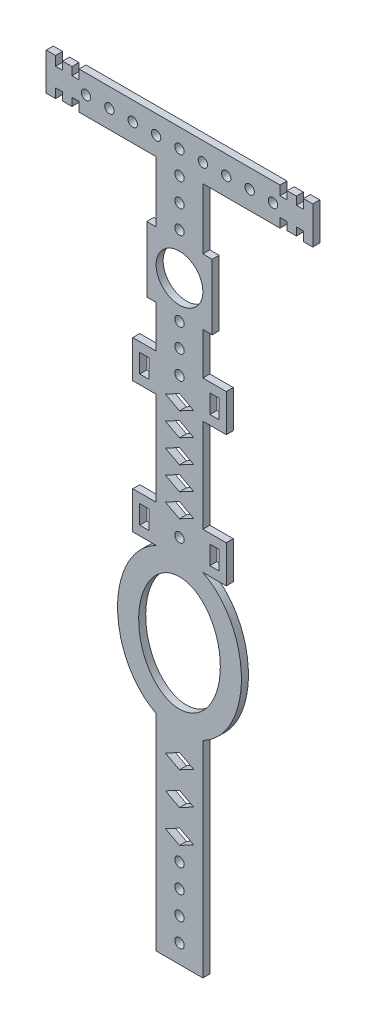
SolidWorks part; units mm, degrees
ref_plane "前视基准面" through (0, 0, 0) normal (0, 0, 1) x (1, 0, 0)
ref_plane "上视基准面" through (0, 0, 0) normal (0, 1, 0) x (1, 0, 0)
ref_plane "右视基准面" through (0, 0, 0) normal (1, 0, 0) x (0, 0, -1)
other "Configuration Table"
sketch "草图1" plane through (0, 0, 0) normal (0, 0, 1) x (1, 0, 0)
  line L0 (-21.4993, 30) -> (-21.4993, 28)
  line L1 (-21.4993, 28) -> (-22.9993, 28)
  line L2 (-22.9993, 29.7) -> (-24.9993, 29.7)
  line L3 (-7, 9) -> (-5, 9)
  line L4 (-7, 9) -> (-7, -5)
  line L5 (-7, -5) -> (-5, -5)
  line L6 (7, 9) -> (7, -5)
  line L7 (-7, 9) -> (7, -5) construction
  line L8 (-7, -5) -> (7, 9) construction
  line L9 (-24.9993, 29.7) -> (-24.9993, 28)
  line L10 (-26.4993, 28) -> (-26.4993, 30.4519)
  line L11 (2.9879, -40.9786) -> (-0.0121, -42.582)
  line L12 (-26.4993, 30) -> (-28.4993, 30)
  line L13 (-28.4993, 30) -> (-28.4993, 22)
  line L18 (-22.9993, 24) -> (-22.9993, 22.3)
  line L19 (-26.4993, 24) -> (-24.9993, 24)
  line L20 (0, -0.8258) -> (0, -11.7354) construction
  line L21 (-5, 9) -> (-5, 22)
  line L22 (-5, 22) -> (-21.4993, 22)
  line L23 (-26.4993, 22) -> (-28.4993, 22)
  line L24 (-26.4993, 24) -> (-26.4993, 22)
  line L25 (-0.0121, -42.582) -> (-3.0121, -40.9786)
  line L26 (-24.9993, 22.3) -> (-24.9993, 24)
  line L27 (-22.9993, 22.3) -> (-24.9993, 22.3)
  line L29 (-21.4993, 24) -> (-22.9993, 24)
  line L30 (-21.4993, 22) -> (-21.4993, 24)
  line L35 (22.9993, 28) -> (22.9993, 29.7)
  line L36 (26.4993, 28) -> (24.9993, 28)
  line L42 (-26.4993, 28) -> (-24.9993, 28)
  line L43 (-22.9993, 28) -> (-22.9993, 29.7)
  line L46 (21.4993, 22) -> (21.4993, 24)
  line L47 (21.4993, 24) -> (22.9993, 24)
  line L48 (-21.4993, 30) -> (21.4993, 30)
  line L49 (-5, -5) -> (-5, -14)
  line L50 (-5, -14) -> (-10, -14)
  line L51 (-10, -14) -> (-10, -22)
  line L52 (-10, -22) -> (-5, -22)
  line L53 (-5, -22) -> (-5, -42)
  line L54 (-5, -42) -> (-10, -42)
  line L55 (-10, -42) -> (-10, -50)
  line L56 (-10, -50) -> (-5, -50)
  line L57 (-8.5, -16) -> (-6.5, -16)
  line L58 (-8.5, -16) -> (-8.5, -20)
  line L59 (-8.5, -20) -> (-6.5, -20)
  line L60 (-6.5, -16) -> (-6.5, -20)
  line L61 (-8.5, -16) -> (-6.5, -20) construction
  line L62 (-8.5, -20) -> (-6.5, -16) construction
  line L63 (-8.5, -44) -> (-6.5, -44)
  line L64 (-8.5, -44) -> (-8.5, -48)
  line L65 (-8.5, -48) -> (-6.5, -48)
  line L66 (-6.5, -44) -> (-6.5, -48)
  line L67 (-8.5, -44) -> (-6.5, -48) construction
  line L68 (-8.5, -48) -> (-6.5, -44) construction
  line L69 (5, 9) -> (5, 22)
  line L70 (22.9993, 22.3) -> (24.9993, 22.3)
  line L71 (24.9993, 22.3) -> (24.9993, 24)
  line L72 (26.4993, 24) -> (26.4993, 22)
  line L73 (-3.0121, -40.9786) -> (-0.0121, -39.3752)
  line L74 (26.4993, 22) -> (28.4993, 22)
  line L75 (26.4993, 24) -> (24.9993, 24)
  line L76 (22.9993, 24) -> (22.9993, 22.3)
  line L77 (28.4993, 30) -> (28.4993, 22)
  line L78 (26.4993, 30) -> (28.4993, 30)
  line L79 (5, 22) -> (21.4993, 22)
  line L80 (5, -5) -> (5, -14)
  line L81 (8.5, -48) -> (6.5, -44) construction
  line L82 (8.5, -44) -> (6.5, -48) construction
  line L83 (8.5, -20) -> (6.5, -16) construction
  line L84 (8.5, -16) -> (6.5, -20) construction
  line L85 (6.5, -44) -> (6.5, -48)
  line L86 (8.5, -48) -> (6.5, -48)
  line L87 (8.5, -44) -> (8.5, -48)
  line L88 (8.5, -44) -> (6.5, -44)
  line L89 (6.5, -16) -> (6.5, -20)
  line L90 (8.5, -20) -> (6.5, -20)
  line L91 (8.5, -16) -> (8.5, -20)
  line L92 (8.5, -16) -> (6.5, -16)
  line L93 (10, -50) -> (5, -50)
  line L94 (10, -42) -> (10, -50)
  line L95 (5, -42) -> (10, -42)
  line L96 (5, -22) -> (5, -42)
  line L97 (10, -22) -> (5, -22)
  line L98 (10, -14) -> (10, -22)
  line L99 (5, -14) -> (10, -14)
  line L100 (-5, -81.1196) -> (-5, -125.1196)
  line L101 (-0.0121, -39.3752) -> (2.9879, -40.9786)
  line L102 (5, -125.1196) -> (5, -81.1196)
  line L107 (3, -101.4579) -> (0, -103.0613)
  line L108 (0, -103.0613) -> (-3, -101.4579)
  line L109 (-3, -101.4579) -> (0, -99.8545)
  line L110 (0, -99.8545) -> (3, -101.4579)
  line L111 (3, -94.4579) -> (0, -96.0613)
  line L112 (0, -96.0613) -> (-3, -94.4579)
  line L113 (-3, -94.4579) -> (0, -92.8545)
  line L114 (0, -92.8545) -> (3, -94.4579)
  line L115 (3, -87.4579) -> (0, -89.0613)
  line L116 (0, -89.0613) -> (-3, -87.4579)
  line L117 (-3, -87.4579) -> (0, -85.8545)
  line L118 (0, -85.8545) -> (3, -87.4579)
  line L119 (-5, -125.1196) -> (5, -125.1196)
  line L120 (-27.5, 26) -> (-15.7949, 26) construction
  line L121 (26.4993, 28) -> (26.4993, 30)
  line L122 (2.9879, -35.9786) -> (-0.0121, -37.582)
  line L123 (24.9993, 29.7) -> (24.9993, 28)
  line L124 (22.9993, 29.7) -> (24.9993, 29.7)
  line L125 (21.4993, 28) -> (22.9993, 28)
  line L126 (21.4993, 30) -> (21.4993, 28)
  line L127 (5, -5) -> (7, -5)
  line L128 (5, 9) -> (7, 9)
  line L129 (-0.0121, -37.582) -> (-3.0121, -35.9786)
  line L130 (-3.0121, -35.9786) -> (-0.0121, -34.3752)
  line L131 (-0.0121, -34.3752) -> (2.9879, -35.9786)
  line L132 (2.9879, -30.9786) -> (-0.0121, -32.582)
  line L133 (-0.0121, -32.582) -> (-3.0121, -30.9786)
  line L134 (-3.0121, -30.9786) -> (-0.0121, -29.3752)
  line L135 (-0.0121, -29.3752) -> (2.9879, -30.9786)
  line L136 (2.9879, -25.9786) -> (-0.0121, -27.582)
  line L137 (-0.0121, -27.582) -> (-3.0121, -25.9786)
  line L138 (-3.0121, -25.9786) -> (-0.0121, -24.3752)
  line L139 (-0.0121, -24.3752) -> (2.9879, -25.9786)
  line L140 (2.9879, -20.9786) -> (-0.0121, -22.582)
  line L141 (-0.0121, -22.582) -> (-3.0121, -20.9786)
  line L142 (-3.0121, -20.9786) -> (-0.0121, -19.3752)
  line L143 (-0.0121, -19.3752) -> (2.9879, -20.9786)
  circle A0 centre (0, 2) radius 5
  circle A2 centre (0, -121.1196) radius 1
  circle A3 centre (0, -116.1196) radius 1
  circle A4 centre (0, -46) radius 1
  circle A10 centre (0, -16) radius 1
  circle A11 centre (0, -11) radius 1
  circle A12 centre (0, -6) radius 1
  circle A13 centre (0, 25.9514) radius 1
  circle A14 centre (5, 25.9514) radius 1
  circle A15 centre (10, 25.9514) radius 1
  circle A16 centre (15, 25.9514) radius 1
  circle A17 centre (20, 25.9514) radius 1
  circle A18 centre (-5, 25.9514) radius 1
  circle A19 centre (-10, 25.9514) radius 1
  circle A20 centre (-15, 25.9514) radius 1
  circle A21 centre (-20, 25.9514) radius 1
  circle A22 centre (0, 20.9514) radius 1
  circle A23 centre (0, 15.9514) radius 1
  circle A24 centre (0, 10.9514) radius 1
  circle A25 centre (0, -111.1196) radius 1
  circle A26 centre (0, -106.1196) radius 1
  circle A27 centre (0, -41) radius 1 [skipped]
  circle A28 centre (0, -36) radius 1 [skipped]
  circle A29 centre (0, -31) radius 1 [skipped]
  circle A30 centre (0, -26) radius 1 [skipped]
  circle A31 centre (0, -21) radius 1 [skipped]
  ellipse E0 centre (0, -65.5598) end of major axis (0, -77.8215) minor radius 8.7277
  spline S1 degree 3 poles (-2.9572, -82.0581) (0, -82.472) (2.9572, -82.0581) (6.5802, -80.4965) (10.1362, -77.0656) (12.461, -72.0885) (13.2579, -67.5921) (13.2579, -63.5275) (12.461, -59.0311) (10.1362, -54.0539) (6.5802, -50.6231) (2.9572, -49.0614) (0, -48.6476) (-2.9572, -49.0614) (-6.5802, -50.6231) (-10.1362, -54.0539) (-12.461, -59.0311) (-13.2579, -63.5275) (-13.2579, -67.5921) (-12.461, -72.0885) (-10.1362, -77.0656) (-6.5802, -80.4965) (-2.9572, -82.0581) (0, -82.472) (2.9572, -82.0581) knots -0.785398 -0.392699 -0.19635 0 0.19635 0.392699 0.785398 1.178097 1.472622 1.668971 1.963495 2.356194 2.748894 2.945243 3.141593 3.337942 3.534292 3.926991 4.31969 4.614214 4.810564 5.105088 5.497787 5.890486 6.086836 6.283185 6.479535 6.675884 7.068583 only from (0, -82.334) to (0, -82.334)
  point P0 (-21.4993, 30)
  point P25 (-28.4993, 26)
  point P26 (0, -41)
  point P34 (-21.4993, 22)
  point P42 (-7.5, -46)
  point P45 (-7.5, -18)
  point P66 (-7.5, -18)
  point P72 (-13.2402, -65.5598)
  point P74 (13.2402, -65.5598)
  point P75 (-5, -50)
  point P81 (0, 30)
  point P107 (5, -50)
  point P108 (7.5, -18)
  point P109 (7.5, -46)
  point P114 (0, -36)
  point P139 (0, -31)
  point P182 (21.4993, 22)
  point P183 (28.4993, 26)
  point P184 (21.4993, 30)
  point P190 (0, -26)
  point P195 (0, -21)
  dimension "D1" = 10
  dimension "D38" = 2
  dimension "D40" = 2
  dimension "D2" = 14
  dimension "D3" = 14
  dimension "D5" = 2
  dimension "D6" = 1.7
  dimension "D7" = 1.5
  dimension "D8" = 2
  dimension "D9" = 4
  dimension "D10" = 2
  dimension "D11" = 8
  dimension "D12" = 3
  dimension "D13" = 2
  dimension "D14" = 4
  dimension "D15" = 5
  dimension "D21" = 5
  dimension "D22" = 8
  dimension "D23" = 1.5
  dimension "D24" = 2
  dimension "D25" = 4
  dimension "D26" = 20
  dimension "D27" = 4
  dimension "D28" = 10
  dimension "D39" = 9
  dimension "D41" = 5
  dimension "D42" = 5
extrude "凸台-拉伸1" add sketch "草图1" along normal blind 1.5 contours S1 L93 L94 L95 L96 L97 L98 L99 L80 L127 L6 L128 L69 L79 L46 L47 L76 L70 L71 L75 L72 L74 L77 L78 L121 L36 L123 L124 L35 L125 L126 L48 L0 L1 L43 L2 L9 L42 L10 L12 L13 L23 L24 L19 L26 L27 L18 L29 L30 L22 L21 | S1 E0 | S1 L100 L119 L102 A26 A25 A3 A2 L109 L110 L107 L108 L113 L114 L111 L112 L117 L118 L115 L116
